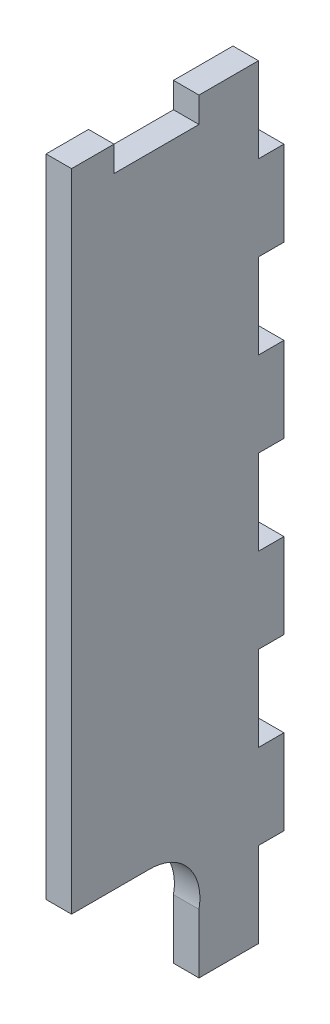
SolidWorks part; units mm, degrees
ref_plane "Front Plane" through (0, 0, 0) normal (0, 0, 1) x (1, 0, 0)
ref_plane "Top Plane" through (0, 0, 0) normal (0, 1, 0) x (1, 0, 0)
ref_plane "Right Plane" through (0, 0, 0) normal (1, 0, 0) x (0, 0, -1)
sketch "Sketch1" plane through (0, 0, 0) normal (1, 0, 0) x (0, 0, -1)
  line L0 (24.704, 12.7205) -> (33.704, 12.7205)
  line L1 (24.704, 88.7205) -> (29.704, 88.7205)
  line L2 (24.704, 88.7205) -> (24.704, 12.7205)
  line L3 (39.704, -1.2795) -> (46.704, -1.2795)
  line L4 (49.704, 78.7205) -> (49.704, 68.7205)
  line L5 (46.704, 8.7205) -> (49.704, 8.7205)
  line L6 (46.704, 8.7205) -> (46.704, -1.2795)
  line L9 (46.704, 28.7205) -> (49.704, 28.7205)
  line L10 (46.704, 28.7205) -> (46.704, 18.7205)
  line L11 (46.704, 18.7205) -> (49.704, 18.7205)
  line L12 (49.704, 18.7205) -> (49.704, 8.7205)
  line L13 (46.704, 48.7205) -> (49.704, 48.7205)
  line L14 (46.704, 48.7205) -> (46.704, 38.7205)
  line L15 (46.704, 38.7205) -> (49.704, 38.7205)
  line L16 (49.704, 38.7205) -> (49.704, 28.7205)
  line L17 (46.704, 68.7205) -> (49.704, 68.7205)
  line L18 (46.704, 68.7205) -> (46.704, 58.7205)
  line L19 (46.704, 58.7205) -> (49.704, 58.7205)
  line L21 (49.704, 58.7205) -> (49.704, 48.7205)
  line L22 (46.704, 88.7205) -> (46.704, 78.7205)
  line L23 (46.704, 78.7205) -> (49.704, 78.7205)
  line L26 (29.704, 88.7205) -> (29.704, 85.7205)
  line L27 (29.704, 85.7205) -> (39.704, 85.7205)
  line L28 (39.704, 88.7205) -> (39.704, 85.7205)
  line L29 (39.704, -1.2795) -> (39.704, 5.7205)
  line L30 (39.704, 88.7205) -> (46.704, 88.7205)
  arc A0 (33.704, 12.7205) -> (39.704, 5.7205) centre (33.9065, 6.8226) cw
  dimension "D1" = 76
  dimension "D2" = 5
  dimension "D3" = 7
  dimension "D4" = 10
  dimension "D5" = 3
  dimension "D6" = 3
  dimension "D7" = 3
  dimension "D8" = 3
  dimension "D9" = 3
  dimension "D10" = 9
  dimension "D11" = 10
  dimension "D12" = 3
  dimension "D13" = 7
  dimension "D14" = 10
  dimension "D15" = 10
  dimension "D16" = 10
  dimension "D17" = 10
  dimension "D18" = 10
  dimension "D19" = 10
  dimension "D20" = 10
  dimension "D21" = 10
extrude "Boss-Extrude1" add sketch "Sketch1" along normal blind 3
